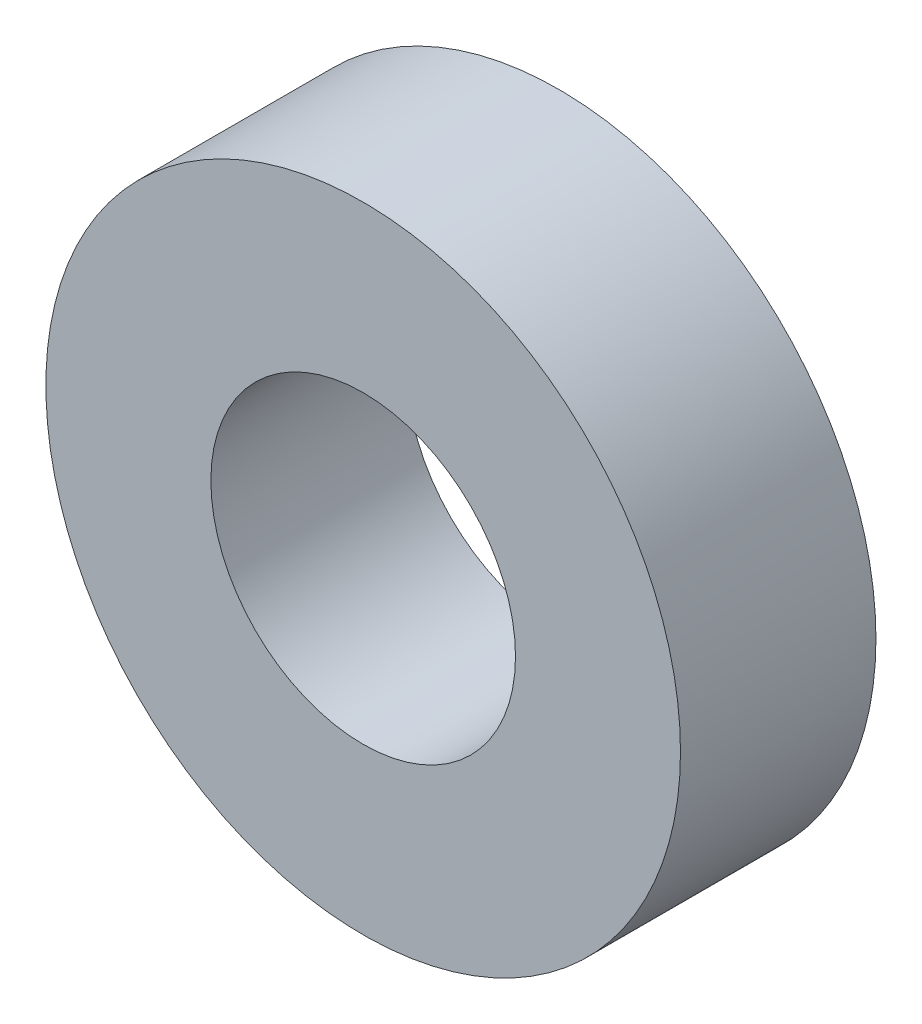
SolidWorks part; units mm, degrees
material "EPDM 60 Durometer"
ref_plane "Front Plane" through (0, 0, 0) normal (0, 0, 1) x (1, 0, 0)
ref_plane "Top Plane" through (0, 0, 0) normal (0, 1, 0) x (1, 0, 0)
ref_plane "Right Plane" through (0, 0, 0) normal (1, 0, 0) x (0, 0, -1)
sketch "Sketch1" plane through (0, 0, 0) normal (0, 0, 1) x (1, 0, 0)
  circle A0 centre (0, 0) radius 1.524
  circle A1 centre (0, 0) radius 3.175
  dimension "ID" = 3.048
  dimension "OD" = 6.35
extrude "Extrude1" add sketch "Sketch1" against normal blind 1.9558
